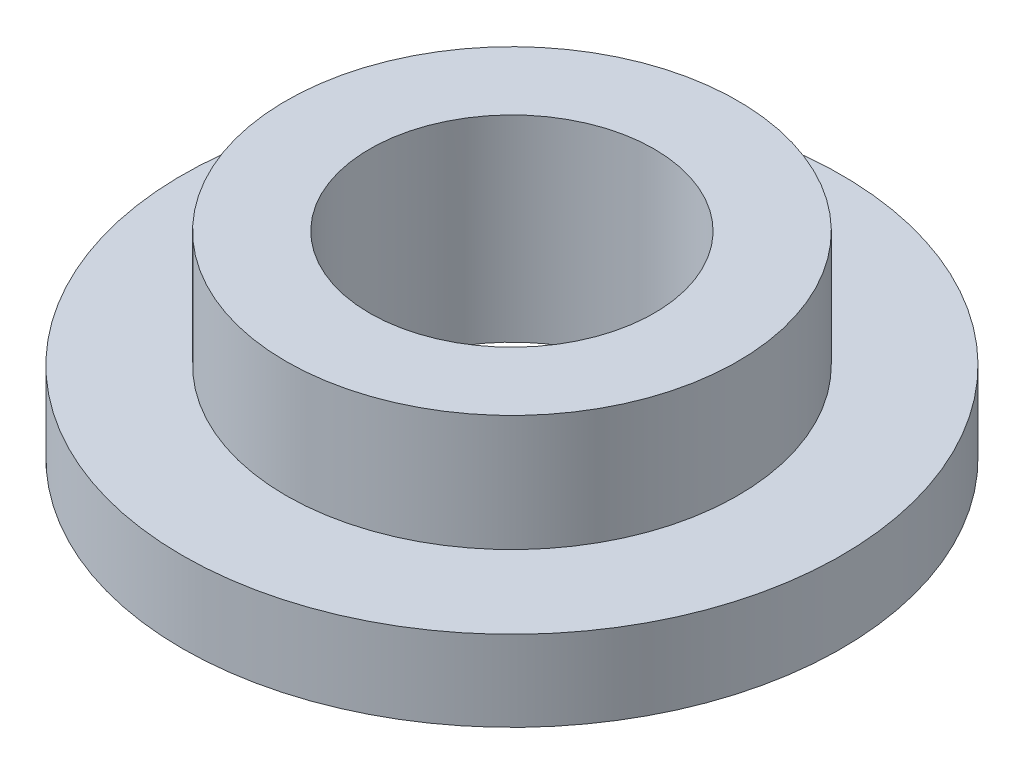
SolidWorks part; units mm, degrees
ref_plane "Front Plane" through (0, 0, 0) normal (0, 0, 1) x (1, 0, 0)
ref_plane "Top Plane" through (0, 0, 0) normal (0, 1, 0) x (1, 0, 0)
ref_plane "Right Plane" through (0, 0, 0) normal (1, 0, 0) x (0, 0, -1)
sketch "Sketch1" plane through (0, 0, 0) normal (0, 1, 0) x (1, 0, 0)
  circle A0 centre (0, 0) radius 13.9
  dimension "D1" = 27.8
extrude "Boss-Extrude1" add sketch "Sketch1" along normal blind 3.4
sketch "Sketch2" plane through (0, 3.4, 0) normal (0, 1, 0) x (1, 0, 0)
  circle A0 centre (0, 0) radius 9.525
  dimension "D1" = 19.05
extrude "Boss-Extrude2" add sketch "Sketch2" along normal blind 4.9
sketch "Sketch3" plane through (0, 0, 0) normal (0, -1, 0) x (1, 0, 0)
  circle A0 centre (0, 0) radius 6
  dimension "D1" = 12
extrude "Cut-Extrude1" cut sketch "Sketch3" against normal up to surface (8.3 mm away) up to face at (0, 8.3, 9.525)
